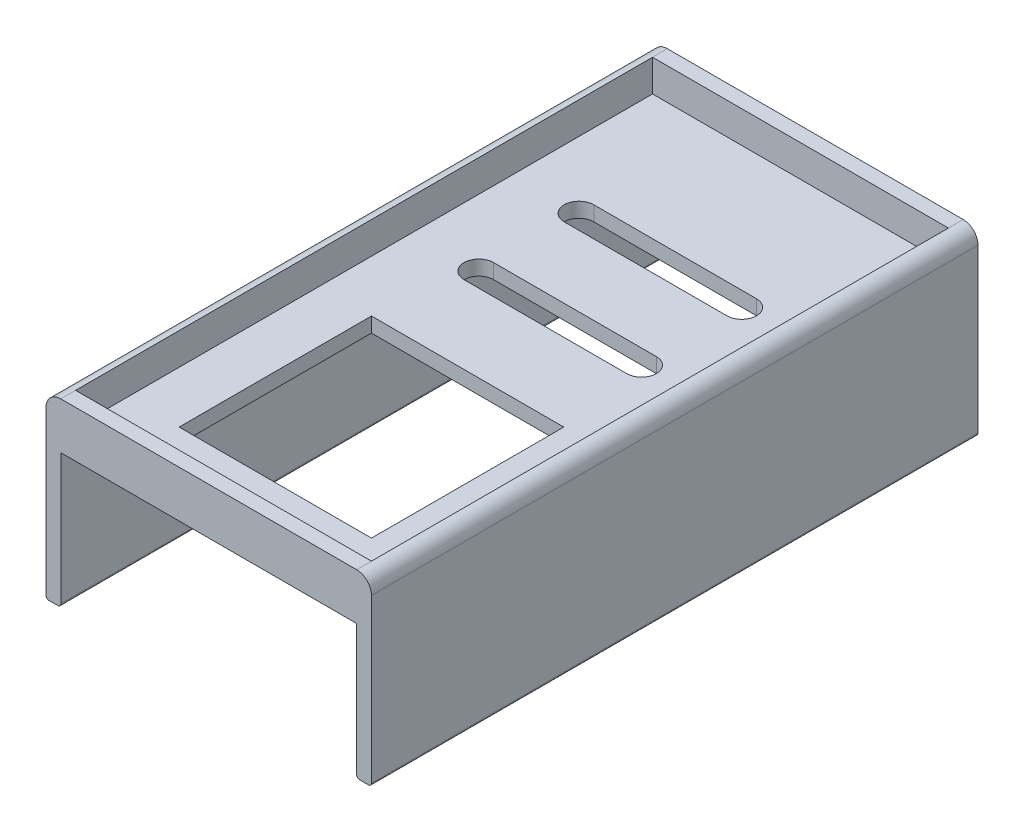
SolidWorks part; units mm, degrees
ref_plane "Front Plane" through (0, 0, 0) normal (0, 0, 1) x (1, 0, 0)
ref_plane "Top Plane" through (0, 0, 0) normal (0, 1, 0) x (1, 0, 0)
ref_plane "Right Plane" through (0, 0, 0) normal (1, 0, 0) x (0, 0, -1)
sketch "Sketch3" plane through (0, 0, 0) normal (0, 0, 1) x (1, 0, 0)
  line L0 (-76.0997, 40.6522) -> (143.9003, 40.6522)
  line L1 (-76.0997, 40.6522) -> (-76.0997, -79.3478)
  line L2 (143.9003, 40.6522) -> (143.9003, -79.3478)
  line L3 (-76.0997, -79.3478) -> (-66.0997, -79.3478)
  line L4 (-66.0997, -79.3478) -> (-66.0997, 9.1522)
  line L5 (143.9003, -79.3478) -> (133.9003, -79.3478)
  line L6 (133.9003, -79.3478) -> (133.9003, 9.1522)
  line L7 (133.9003, 9.1522) -> (-66.0997, 9.1522)
  dimension "D1" = 220
  dimension "D2" = 120
  dimension "D3" = 120
  dimension "D4" = 10
  dimension "D5" = 31.5
  dimension "D6" = 10
extrude "Boss-Extrude1" add sketch "Sketch3" against normal blind 410
sketch "Sketch4" plane through (0, 40.6522, 0) normal (0, 1, 0) x (1, 0, 0)
  line L0 (-76.0997, 0) -> (-76.0997, 410)
  line L1 (-76.0997, 410) -> (143.9003, 410)
  line L2 (143.9003, 410) -> (143.9003, 0)
  line L3 (143.9003, 0) -> (-76.0997, 0)
  line L4 (-76.0997, 400) -> (143.9003, 400)
  line L5 (-76.0997, 10) -> (143.9003, 10)
  line L6 (-66.0997, 400) -> (-66.0997, 10)
  line L7 (133.9003, 400) -> (133.9003, 10)
  dimension "D1" = 10
  dimension "D2" = 10
  dimension "D3" = 10
  dimension "D4" = 10
extrude "Cut-Extrude1" cut sketch "Sketch4" against normal blind 21.5 contours L7 L4 L6 L5
sketch "Sketch5" plane through (0, 19.1522, 0) normal (0, 1, 0) x (1, 0, 0)
  line L0 (-66.0997, 400) -> (-66.0997, 10)
  line L1 (-31.0997, 175) -> (98.9003, 175)
  line L2 (-31.0997, 175) -> (-31.0997, 45)
  line L3 (-31.0997, 45) -> (98.9003, 45)
  line L4 (98.9003, 175) -> (98.9003, 45)
  line L5 (-66.0997, 10) -> (133.9003, 10)
  line L6 (133.9003, 10) -> (133.9003, 400)
  line L7 (133.9003, 400) -> (-66.0997, 400)
  line L8 (-21.0997, 237.5528) -> (88.9003, 237.5528) construction
  line L9 (-21.0997, 247.5528) -> (88.9003, 247.5528)
  line L10 (-21.0997, 227.5528) -> (88.9003, 227.5528)
  line L11 (-21.0997, 305.2666) -> (88.9003, 305.2666) construction
  line L12 (-21.0997, 315.2666) -> (88.9003, 315.2666)
  line L13 (-21.0997, 295.2666) -> (88.9003, 295.2666)
  arc A0 (-21.0997, 247.5528) -> (-21.0997, 227.5528) centre (-21.0997, 237.5528) ccw
  arc A1 (88.9003, 227.5528) -> (88.9003, 247.5528) centre (88.9003, 237.5528) ccw
  arc A2 (-21.0997, 315.2666) -> (-21.0997, 295.2666) centre (-21.0997, 305.2666) ccw
  arc A3 (88.9003, 295.2666) -> (88.9003, 315.2666) centre (88.9003, 305.2666) ccw
  point P14 (33.9003, 237.5528)
  point P19 (-31.0997, 237.5528)
  point P22 (33.9003, 305.2666)
  dimension "D7" = 110
  dimension "D10" = 10
  dimension "D11" = 20
  dimension "D1" = 130
  dimension "D2" = 130
  dimension "D3" = 200
  dimension "D4" = 35
  dimension "D5" = 35
  dimension "D6" = 20
  dimension "D8" = 35
  dimension "D9" = 110
extrude "Cut-Extrude2" cut sketch "Sketch5" against normal blind 30 contours L2 L1 L4 L3 | L10 A1 L9 A0 | L13 A3 L12 A2
sketch "Sketch6" plane through (0, 0, 0) normal (0, 0, 1) x (1, 0, 0)
  line L0 (-76.0997, 30.6522) -> (-76.0997, -77.3478)
  line L1 (-74.0997, -79.3478) -> (-68.0997, -79.3478)
  line L2 (-66.0997, -77.3478) -> (-66.0997, 9.1522)
  line L3 (-66.0997, 9.1522) -> (133.9003, 9.1522)
  line L4 (133.9003, 9.1522) -> (133.9003, -77.3478)
  line L5 (135.9003, -79.3478) -> (141.9003, -79.3478)
  line L6 (143.9003, -77.3478) -> (143.9003, 30.6522)
  line L7 (133.9003, 40.6522) -> (-66.0997, 40.6522)
  line L8 (-76.0997, 40.6522) -> (-76.0997, 30.6522)
  line L9 (-66.0997, 40.6522) -> (-76.0997, 40.6522)
  line L10 (133.9003, 40.6522) -> (143.9003, 40.6522)
  line L11 (143.9003, 40.6522) -> (143.9003, 30.6522)
  line L12 (143.9003, 30.6522) -> (143.9003, 40.6522)
  line L13 (143.9003, -77.3478) -> (143.9003, -79.3478)
  line L14 (143.9003, -79.3478) -> (141.9003, -79.3478)
  line L15 (133.9003, -77.3478) -> (133.9003, -79.3478)
  line L16 (133.9003, -79.3478) -> (135.9003, -79.3478)
  line L17 (-66.0997, -77.3478) -> (-66.0997, -79.3478)
  line L18 (-66.0997, -79.3478) -> (-68.0997, -79.3478)
  line L19 (-74.0997, -79.3478) -> (-76.0997, -79.3478)
  line L20 (-76.0997, -79.3478) -> (-76.0997, -77.3478)
  arc A0 (143.9003, 30.6522) -> (133.9003, 40.6522) centre (133.9003, 30.6522) ccw
  arc A1 (-76.0997, 30.6522) -> (-66.0997, 40.6522) centre (-66.0997, 30.6522) cw
  arc A2 (141.9003, -79.3478) -> (143.9003, -77.3478) centre (141.9003, -77.3478) ccw
  arc A3 (135.9003, -79.3478) -> (133.9003, -77.3478) centre (135.9003, -77.3478) cw
  arc A4 (-68.0997, -79.3478) -> (-66.0997, -77.3478) centre (-68.0997, -77.3478) ccw
  arc A5 (-74.0997, -79.3478) -> (-76.0997, -77.3478) centre (-74.0997, -77.3478) cw
  point P18 (143.9003, 40.6522)
  point P21 (-76.0997, 40.6522)
  point P24 (143.9003, -79.3478)
  point P27 (133.9003, -79.3478)
  point P30 (-66.0997, -79.3478)
  point P33 (-76.0997, -79.3478)
  dimension "D1" = 10
  dimension "D2" = 2
sketch "Sketch9" plane through (0, -79.3478, 0) normal (0, -1, 0) x (1, 0, 0)
  line L1 (143.9003, -410) -> (133.9003, -410)
  line L2 (143.9003, -410) -> (143.9003, 0)
  line L3 (143.9003, 0) -> (133.9003, 0)
  line L4 (133.9003, -410) -> (133.9003, 0)
extrude "Boss-Extrude2" add sketch "Sketch9" along normal blind 2
sketch "Sketch10" plane through (0, -79.3478, 0) normal (0, -1, 0) x (1, 0, 0)
  line L1 (-66.0997, -410) -> (-76.0997, -410)
  line L2 (-66.0997, -410) -> (-66.0997, 0)
  line L3 (-66.0997, 0) -> (-76.0997, 0)
  line L4 (-76.0997, -410) -> (-76.0997, 0)
extrude "Boss-Extrude3" add sketch "Sketch10" along normal blind 2
sketch "Sketch11" plane through (0, 0, 0) normal (0, 0, 1) x (1, 0, 0)
  line L0 (-76.0997, 30.6522) -> (-76.0997, -79.3478)
  line L1 (-74.0997, -81.3478) -> (-68.0997, -81.3478)
  line L2 (-66.0997, -79.3478) -> (-66.0997, 9.1522)
  line L3 (-66.0997, 9.1522) -> (133.9003, 9.1522)
  line L4 (133.9003, 9.1522) -> (133.9003, -79.3478)
  line L5 (135.9003, -81.3478) -> (141.9003, -81.3478)
  line L6 (143.9003, -79.3478) -> (143.9003, 30.6522)
  line L7 (133.9003, 40.6522) -> (-66.0997, 40.6522)
  line L8 (-76.0997, 30.6522) -> (-76.0997, 40.6522)
  line L9 (-76.0997, 40.6522) -> (-66.0997, 40.6522)
  line L10 (133.9003, 40.6522) -> (143.9003, 40.6522)
  line L11 (143.9003, 40.6522) -> (143.9003, 30.6522)
  line L12 (143.9003, -79.3478) -> (143.9003, -81.3478)
  line L13 (143.9003, -81.3478) -> (141.9003, -81.3478)
  line L14 (135.9003, -81.3478) -> (133.9003, -81.3478)
  line L15 (133.9003, -81.3478) -> (133.9003, -79.3478)
  line L16 (-66.0997, -79.3478) -> (-66.0997, -81.3478)
  line L17 (-66.0997, -81.3478) -> (-68.0997, -81.3478)
  line L18 (-74.0997, -81.3478) -> (-76.0997, -81.3478)
  line L19 (-76.0997, -81.3478) -> (-76.0997, -79.3478)
  line L20 (-76.0997, 30.6522) -> (-76.0997, 40.6522)
  line L21 (-76.0997, 40.6522) -> (-66.0997, 40.6522)
  arc A0 (143.9003, 30.6522) -> (133.9003, 40.6522) centre (133.9003, 30.6522) ccw
  arc A1 (-76.0997, 30.6522) -> (-66.0997, 40.6522) centre (-66.0997, 30.6522) cw
  arc A2 (141.9003, -81.3478) -> (143.9003, -79.3478) centre (141.9003, -79.3478) ccw
  arc A3 (135.9003, -81.3478) -> (133.9003, -79.3478) centre (135.9003, -79.3478) cw
  arc A4 (-68.0997, -81.3478) -> (-66.0997, -79.3478) centre (-68.0997, -79.3478) ccw
  arc A5 (-76.0997, -79.3478) -> (-74.0997, -81.3478) centre (-74.0997, -79.3478) ccw
  point P18 (143.9003, 40.6522)
  point P21 (-76.0997, 40.6522)
  point P24 (143.9003, -81.3478)
  point P27 (133.9003, -81.3478)
  point P30 (-66.0997, -81.3478)
  point P33 (-76.0997, -81.3478)
  line M15 (-76.0997, 40.6522) -> (-76.0997, -81.3478)
  line M16 (-76.0997, -81.3478) -> (-66.0997, -81.3478)
  line M17 (-66.0997, -81.3478) -> (-66.0997, 9.1522)
  line M19 (133.9003, 9.1522) -> (133.9003, -81.3478)
  line M20 (133.9003, -81.3478) -> (143.9003, -81.3478)
  line M21 (143.9003, -81.3478) -> (143.9003, 40.6522)
  line M22 (143.9003, 40.6522) -> (-76.0997, 40.6522)
  dimension "D1" = 10
  dimension "D2" = 2
extrude "Cut-Extrude4" cut sketch "Sketch11" against normal blind 600 contours A1 M15 M22 | A0 M21 M22 | A2 M20 M21 | A3 M20 M19 | A5 M15 M16 | A4 M16 M17
